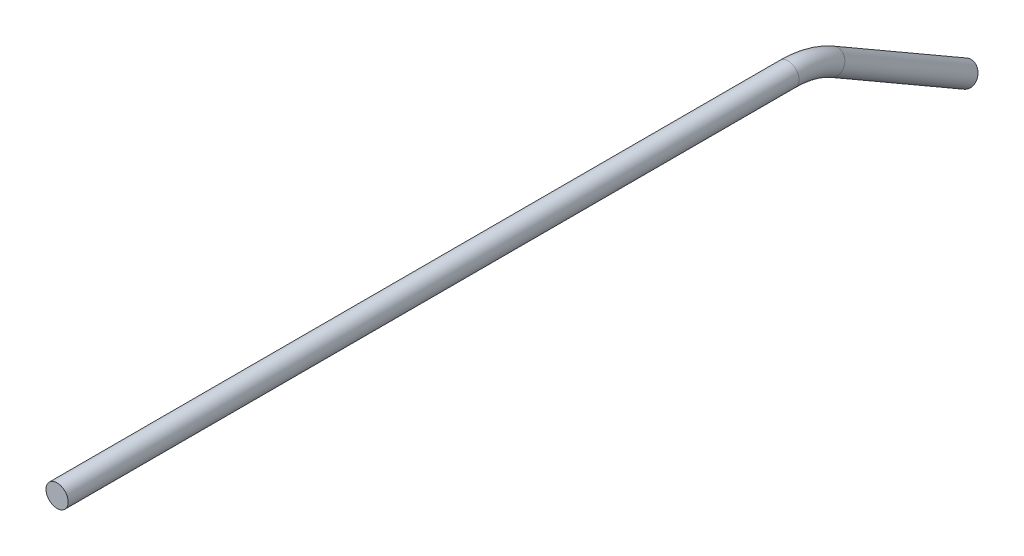
SolidWorks part; units mm, degrees
ref_plane "Front Plane" through (0, 0, 0) normal (0, 0, 1) x (1, 0, 0)
ref_plane "Top Plane" through (0, 0, 0) normal (0, 1, 0) x (1, 0, 0)
ref_plane "Right Plane" through (0, 0, 0) normal (1, 0, 0) x (0, 0, -1)
sketch "Sketch2" plane through (0, 0, 0) normal (0, 0, 1) x (1, 0, 0)
  circle A0 centre (0, 0) radius 3.175
  dimension "D1" = 6.35
sketch "Sketch4" plane through (0, 0, 0) normal (1, 0, 0) x (0, 0, -1)
  line L0 (0, 0) -> (209.0941, 0)
  line L1 (221.7941, -3.403) -> (259.8941, -25.4)
  arc A0 (221.7941, -3.403) -> (209.0941, 0) centre (209.0941, -25.4) ccw
  point P6 (215.9, 0)
  dimension "D4" = 25.4
  dimension "D1" = 215.9
  dimension "D2" = 50.8
  dimension "D3" = 30
sweep "Sweep1" add profiles "Sketch2" path "Sketch4"
